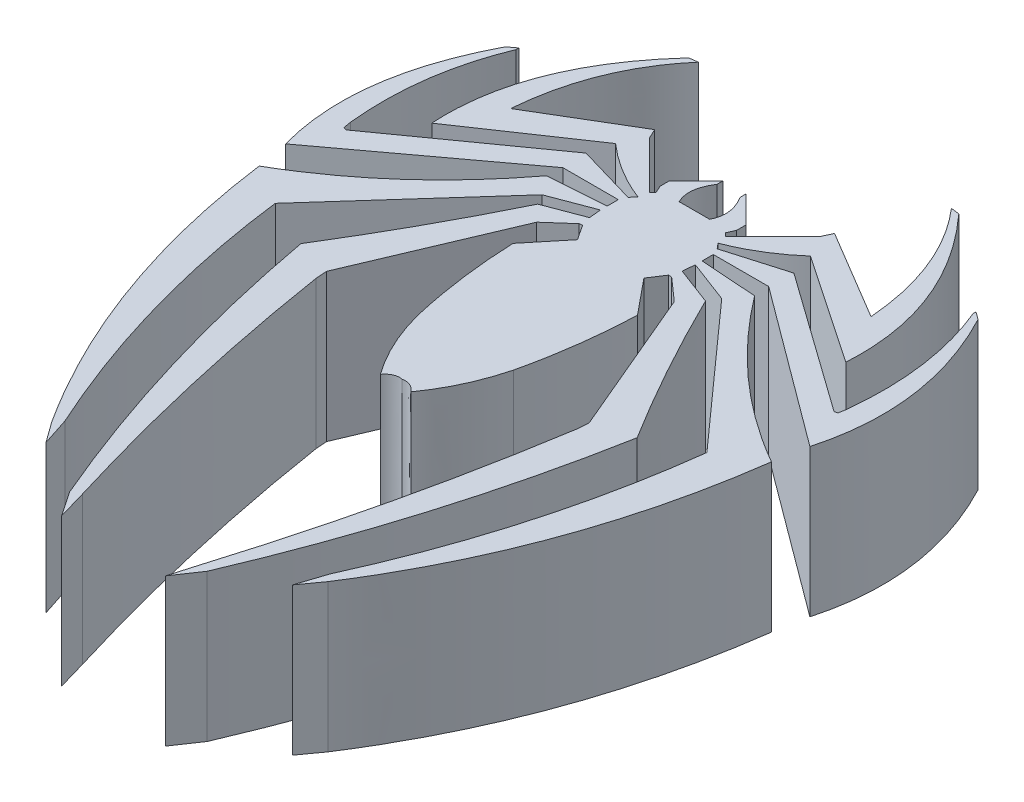
SolidWorks part; units mm, degrees
ref_plane "Front Plane" through (0, 0, 0) normal (0, 0, 1) x (1, 0, 0)
ref_plane "Top Plane" through (0, 0, 0) normal (0, 1, 0) x (1, 0, 0)
ref_plane "Right Plane" through (0, 0, 0) normal (1, 0, 0) x (0, 0, -1)
sketch "Sketch1" plane through (0, 0, 0) normal (0, 1, 0) x (1, 0, 0)
  line L0 (-10.9783, 13.6155) -> (28.9533, 13.6155) construction
  line L1 (-0.7748, 18.2055) -> (-2.5913, 16.3889)
  line L6 (-25, -25) -> (25, 25) construction
  line L7 (-25, 25) -> (25, -25) construction
  line L8 (-2.5913, 16.3889) -> (-2.5913, 15.7513)
  line L9 (-2.5913, 15.7513) -> (-2.3628, 15.246)
  line L10 (-2.3628, 15.246) -> (-2.5913, 15.0175)
  line L11 (-2.5913, 15.0175) -> (-5.7793, 18.2055)
  line L12 (-5.7793, 18.2055) -> (-6.0953, 18.8929)
  line L13 (-6.0953, 18.8929) -> (-12.2188, 15.246)
  line L14 (-8.5819, 24.3333) -> (-9.157, 24.2594)
  line L15 (-14.0377, 11.7189) -> (-6.6068, 16.7487)
  line L16 (-3.0229, 14.0118) -> (-2.714, 14.3731)
  line L17 (-3.0229, 14.0118) -> (-7.0484, 15.186)
  line L18 (-7.0484, 15.186) -> (-16.5423, 8.415)
  line L19 (-16.5423, 8.415) -> (-16.7502, 8.4756)
  line L20 (-16.7502, 8.4756) -> (-16.844, 8.9994)
  line L21 (-15.4983, 18.8929) -> (-15.4983, 19.0835)
  line L22 (-15.4983, 19.0835) -> (-15.7555, 18.8929)
  line L23 (-15.7555, 18.8929) -> (-16.0182, 18.6982)
  line L24 (-17.7726, 5.5454) -> (-6.9764, 13.5466)
  line L25 (-6.9764, 13.5466) -> (-3.2207, 13.5466)
  line L26 (0, 25) -> (0, -4.3272)
  line L27 (-0.7748, 18.2055) -> (-0.7748, 17.8056)
  line L28 (-1.0314, 15.4895) -> (1.0314, 15.4895)
  line L29 (-3.2207, 13.5466) -> (-3.2207, 12.7879)
  line L30 (-3.2207, 12.7879) -> (-7.0484, 12.5231)
  line L31 (-9.3667, -18.7235) -> (-8.3608, -20.1157)
  line L32 (-8.3608, -20.1157) -> (-8.9846, -18.2115)
  line L33 (-14.6322, 1.7022) -> (-6.0953, 11.2457)
  line L34 (-6.0953, 11.2457) -> (-3.2207, 12.3347)
  line L35 (-3.2207, 12.3347) -> (-3.1373, 11.5175)
  line L36 (-3.1373, 11.5175) -> (-5.6883, 10.5511)
  line L37 (-4.6633, -22.2076) -> (-3.5264, -23.8843)
  line L38 (-3.5264, -23.8843) -> (-4.0949, -21.9206)
  line L39 (-8.8427, -1.3327) -> (-8.9014, -0.5524)
  line L40 (-8.9014, -0.5524) -> (-4.6633, 9.4599)
  line L41 (-4.6633, 9.4599) -> (-3.1373, 10.8087)
  line L42 (-3.1373, 10.8087) -> (-2.9186, 10.8252)
  line L43 (-2.9186, 10.8252) -> (-2.254, 9.8094)
  line L44 (-2.254, 9.8094) -> (-4.2194, 7.4088)
  line L46 (2.254, 9.8094) -> (4.2194, 7.4088)
  line L47 (2.9186, 10.8252) -> (2.254, 9.8094)
  line L48 (3.1373, 10.8087) -> (2.9186, 10.8252)
  line L49 (4.6633, 9.4599) -> (3.1373, 10.8087)
  line L50 (8.9014, -0.5524) -> (4.6633, 9.4599)
  line L51 (8.8427, -1.3327) -> (8.9014, -0.5524)
  line L52 (3.5264, -23.8843) -> (4.0949, -21.9206)
  line L53 (4.6633, -22.2076) -> (3.5264, -23.8843)
  line L54 (3.1373, 11.5175) -> (5.6883, 10.5511)
  line L55 (3.2207, 12.3347) -> (3.1373, 11.5175)
  line L56 (6.0953, 11.2457) -> (3.2207, 12.3347)
  line L57 (14.6322, 1.7022) -> (6.0953, 11.2457)
  line L58 (8.3608, -20.1157) -> (8.9846, -18.2115)
  line L59 (9.3667, -18.7235) -> (8.3608, -20.1157)
  line L60 (3.2207, 12.7879) -> (7.0484, 12.5231)
  line L61 (3.2207, 13.5466) -> (3.2207, 12.7879)
  line L62 (0.7748, 18.2055) -> (0.7748, 17.8056)
  line L63 (6.9764, 13.5466) -> (3.2207, 13.5466)
  line L64 (17.7726, 5.5454) -> (6.9764, 13.5466)
  line L65 (15.7555, 18.8929) -> (16.0182, 18.6982)
  line L66 (15.4983, 19.0835) -> (15.7555, 18.8929)
  line L67 (15.4983, 18.8929) -> (15.4983, 19.0835)
  line L68 (16.7502, 8.4756) -> (16.844, 8.9994)
  line L69 (16.5423, 8.415) -> (16.7502, 8.4756)
  line L70 (7.0484, 15.186) -> (16.5423, 8.415)
  line L71 (3.0229, 14.0118) -> (7.0484, 15.186)
  line L72 (3.0229, 14.0118) -> (2.714, 14.3731)
  line L73 (14.0377, 11.7189) -> (6.6068, 16.7487)
  line L74 (8.5819, 24.3333) -> (9.157, 24.2594)
  line L75 (6.0953, 18.8929) -> (12.2188, 15.246)
  line L76 (5.7793, 18.2055) -> (6.0953, 18.8929)
  line L77 (2.5913, 15.0175) -> (5.7793, 18.2055)
  line L78 (2.3628, 15.246) -> (2.5913, 15.0175)
  line L79 (2.5913, 15.7513) -> (2.3628, 15.246)
  line L80 (2.5913, 16.3889) -> (2.5913, 15.7513)
  line L82 (0.7748, 18.2055) -> (2.5913, 16.3889)
  spline S0 degree 2 poles (-12.2188, 15.246) (-11.7787, 20.6207) (-8.5819, 24.3333) knots 0 0 0 1 1 1
  spline S1 degree 2 poles (-9.157, 24.2594) (-14.4477, 18.459) (-14.0377, 11.7189) knots 0 0 0 1 1 1
  spline S2 degree 2 poles (-6.6068, 16.7487) (-4.8416, 15.1968) (-2.714, 14.3731) knots 0 0 0 1 1 1
  spline S3 degree 2 poles (-16.844, 8.9994) (-17.3983, 14.2881) (-15.4983, 18.8929) knots 0 0 0 0.937492 0.937492 0.937492
  spline S4 degree 2 poles (-16.0182, 18.6982) (-19.5486, 11.9642) (-17.7726, 5.5454) knots 0 0 0 1 1 1
  spline S5 degree 2 poles (-0.7748, 17.8056) (-1.5702, 16.533) (-1.0314, 15.4895) knots 0 0 0 1 1 1
  spline S6 degree 2 poles (-7.0484, 12.5231) (-11.3783, 6.7861) (-17.3683, 3.3443) knots 0 0 0 1 1 1
  spline S7 degree 2 poles (-17.3683, 3.3443) (-15.6971, -9.0634) (-9.157, -19.046) knots 0 0 0 1 1 1
  spline S8 degree 2 poles (-8.9846, -18.2115) (-13.3674, -8.5654) (-14.6322, 1.7022) knots 0 0 0 0.965611 0.965611 0.965611
  spline S9 degree 2 poles (-5.6883, 10.5511) (-8.2898, 5.2304) (-11.3983, 0.2073) knots 0 0 0 0.941866 0.941866 0.941866
  spline S10 degree 2 poles (-11.3983, 0.2073) (-9.2259, -11.6308) (-4.5176, -22.5471) knots 0 0 0 1 1 1
  spline S11 degree 2 poles (-4.0949, -21.9206) (-7.2017, -11.7674) (-8.8427, -1.3327) knots 0 0 0 0.957756 0.957756 0.957756
  spline S12 degree 2 poles (-4.2194, 7.4088) (-4.0621, 3.183) (-3.0229, -0.8773) knots 0 0 0 1 1 1
  spline S13 degree 2 poles (-3.2367, 0) (-2.5567, -2.64) (-1.0314, -4.7734) knots 0 0 0 0.876843 0.876843 0.876843
  spline S14 degree 2 poles (-1.0314, -4.7734) (-0.5826, -4.2065) (0, -4.3272) knots 0 0 0 1 1 1
  spline S15 degree 2 poles (1.0314, -4.7734) (0.5826, -4.2065) (0, -4.3272) knots 0 0 0 1 1 1
  spline S16 degree 2 poles (3.2367, 0) (2.5567, -2.64) (1.0314, -4.7734) knots 0 0 0 0.876843 0.876843 0.876843
  spline S17 degree 2 poles (4.2194, 7.4088) (4.0621, 3.183) (3.0229, -0.8773) knots 0 0 0 1 1 1
  spline S18 degree 2 poles (4.0949, -21.9206) (7.2017, -11.7674) (8.8427, -1.3327) knots 0 0 0 0.957756 0.957756 0.957756
  spline S19 degree 2 poles (11.3983, 0.2073) (9.2259, -11.6308) (4.5176, -22.5471) knots 0 0 0 1 1 1
  spline S20 degree 2 poles (5.6883, 10.5511) (8.2898, 5.2304) (11.3983, 0.2073) knots 0 0 0 0.941866 0.941866 0.941866
  spline S21 degree 2 poles (8.9846, -18.2115) (13.3674, -8.5654) (14.6322, 1.7022) knots 0 0 0 0.965611 0.965611 0.965611
  spline S22 degree 2 poles (17.3683, 3.3443) (15.6971, -9.0634) (9.157, -19.046) knots 0 0 0 1 1 1
  spline S23 degree 2 poles (7.0484, 12.5231) (11.3783, 6.7861) (17.3683, 3.3443) knots 0 0 0 1 1 1
  spline S24 degree 2 poles (0.7748, 17.8056) (1.5702, 16.533) (1.0314, 15.4895) knots 0 0 0 1 1 1
  spline S25 degree 2 poles (16.0182, 18.6982) (19.5486, 11.9642) (17.7726, 5.5454) knots 0 0 0 1 1 1
  spline S26 degree 2 poles (16.844, 8.9994) (17.3983, 14.2881) (15.4983, 18.8929) knots 0 0 0 0.937492 0.937492 0.937492
  spline S27 degree 2 poles (6.6068, 16.7487) (4.8416, 15.1968) (2.714, 14.3731) knots 0 0 0 1 1 1
  spline S28 degree 2 poles (9.157, 24.2594) (14.4477, 18.459) (14.0377, 11.7189) knots 0 0 0 1 1 1
  spline S29 degree 2 poles (12.2188, 15.246) (11.7787, 20.6207) (8.5819, 24.3333) knots 0 0 0 1 1 1
  point P2 (0, 0)
  point P30 (-2.254, 16.7262)
  dimension "D44" = 10.09
  dimension "D1" = 50
  dimension "D2" = 50
  dimension "D3" = 0.2073
  dimension "D4" = 1.7022
  dimension "D6" = 3.3443
  dimension "D7" = 3.4102
  dimension "D8" = 5.5454
  dimension "D9" = 5.8517
  dimension "D10" = 7.4088
  dimension "D11" = 8.415
  dimension "D12" = 8.4756
  dimension "D13" = 8.9994
  dimension "D14" = 9.4599
  dimension "D15" = 9.8094
  dimension "D16" = 10.5511
  dimension "D17" = 10.8087
  dimension "D18" = 10.8252
  dimension "D19" = 11.2457
  dimension "D20" = 11.5175
  dimension "D21" = 11.7189
  dimension "D22" = 11.9821
  dimension "D23" = 12.3347
  dimension "D24" = 12.5231
  dimension "D25" = 12.7879
  dimension "D26" = 13.5466
  dimension "D27" = 13.6155
  dimension "D28" = 14.0118
  dimension "D29" = 14.3731
  dimension "D30" = 14.4027
  dimension "D31" = 15.0175
  dimension "D32" = 15.186
  dimension "D33" = 15.246
  dimension "D34" = 15.4895
  dimension "D35" = 15.5388
  dimension "D36" = 15.7513
  dimension "D37" = 16.3889
  dimension "D38" = 16.7487
  dimension "D39" = 17.8056
  dimension "D40" = 18.2055
  dimension "D41" = 18.6982
  dimension "D42" = 18.8929
  dimension "D43" = 19.0835
  dimension "D45" = 24.2594
  dimension "D46" = 24.3333
  dimension "D47" = 13.4379
  dimension "D48" = 0.5524
  dimension "D49" = 0.8773
  dimension "D50" = 1.3327
  dimension "D51" = 4.3063
  dimension "D52" = 4.3272
  dimension "D53" = 4.7734
  dimension "D55" = 18.2115
  dimension "D56" = 18.7235
  dimension "D57" = 19.046
  dimension "D58" = 20.1157
  dimension "D59" = 21.9206
  dimension "D60" = 22.2076
  dimension "D61" = 22.5471
  dimension "D62" = 23.8843
extrude "Boss-Extrude1" add sketch "Sketch1" along normal blind 10 contours S29 L75 L76 L77 L78 L79 L80 L82 L62 S24 L28 L26 S15 S16 S17 L46 L47 L48 L49 L50 L51 S18 L52 L53 S19 S20 L54 L55 L56 L57 S21 L58 L59 S22 S23 L60 L61 L63 L64 S25 L65 L66 L67 S26 L68 L69 L70 L71 L72 S27 L73 | S13 S14 L26 L28 S5 L27 L1 L8 L9 L10 L11 L12 L13 S0 L14 S1 L15 S2 L16 L17 L18 L19 L20 S3 L21 L22 L23 S4 L24 L25 L29 L30 S6 S7 L31 L32 S8 L33 L34 L35 L36 S9 S10 L37 L38 S11 L39 L40 L41 L42 L43
